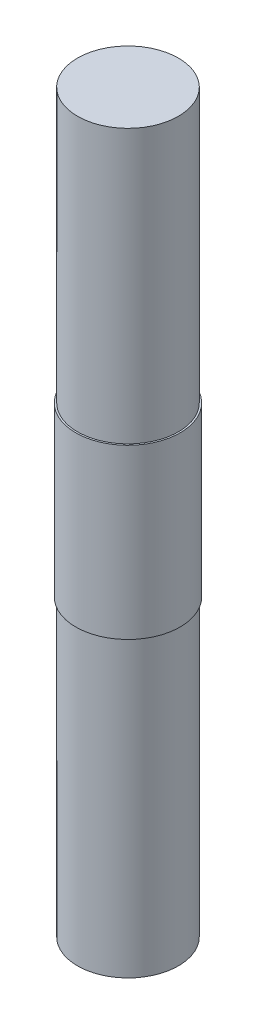
SolidWorks part; units mm, degrees
ref_plane "Front Plane" through (0, 0, 0) normal (0, 0, 1) x (1, 0, 0)
ref_plane "Top Plane" through (0, 0, 0) normal (0, 1, 0) x (1, 0, 0)
ref_plane "Right Plane" through (0, 0, 0) normal (1, 0, 0) x (0, 0, -1)
sketch "Sketch1" plane through (0, 0, 0) normal (0, 0, 1) x (1, 0, 0)
  line L0 (0, 0) -> (0, -52.5)
  line L1 (0, 0) -> (6, 0)
  line L4 (6, 0) -> (6, -30)
  line L7 (6, -52.5) -> (6.2, -52.5)
  line L8 (6.2, -32.5) -> (6.2, -52.5)
  line L9 (6, -30) -> (6, -32.5)
  line L10 (6, -32.5) -> (6.2, -32.5)
  line L13 (0, -52.5) -> (0, -87.5)
  line L14 (0, -87.5) -> (6, -87.5)
  line L15 (6, -52.5) -> (6, -87.5)
  dimension "D5" = 30
  dimension "D2" = 2.5
  dimension "D1" = 6
  dimension "D3" = 20
  dimension "D4" = 6.2
  dimension "D6" = 6
  dimension "D7" = 35
revolve "Revolve4" add sketch "Sketch1" angle 360 about L0
